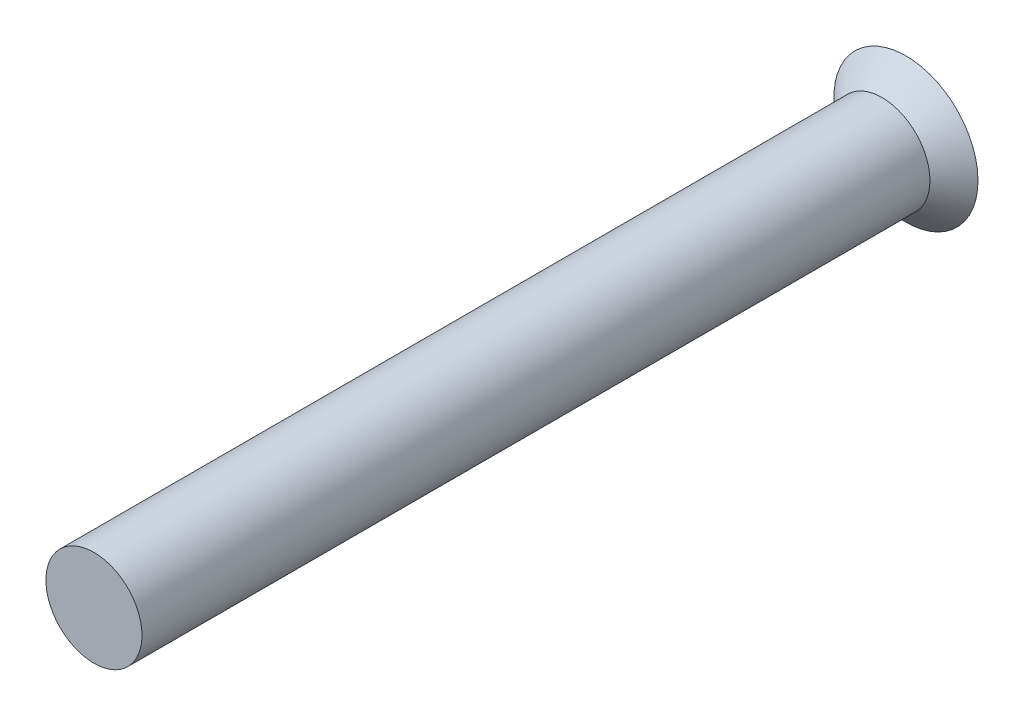
SolidWorks part; units mm, degrees
material "AISI 1020 Steel, Cold Rolled"
ref_plane "Front Plane" through (0, 0, 0) normal (0, 0, 1) x (1, 0, 0)
ref_plane "Top Plane" through (0, 0, 0) normal (0, 1, 0) x (1, 0, 0)
ref_plane "Right Plane" through (0, 0, 0) normal (1, 0, 0) x (0, 0, -1)
sketch "Sketch1" plane through (0, 0, 0) normal (0, 0, 1) x (1, 0, 0)
  circle A0 centre (0, 0) radius 0.5
  dimension "D1" = 1
extrude "Boss-Extrude1" add sketch "Sketch1" along normal mid plane 8.2 contours A0
sketch "Sketch2" plane through (0, 0, 0) normal (1, 0, 0) x (0, 0, -1)
  line L1 (4.35, 0.75) -> (4.35, 0)
  line L2 (4.35, 0) -> (4.1, 0)
  line L3 (4.1, -0.5) -> (4.1, 0.5) construction
  line L4 (4.1, 0) -> (4.1, 0.5)
  line L5 (4.1, 0.5) -> (4.35, 0.75)
  dimension "D1" = 0.25
ref_axis "Axis1" through (0, 0, 2.0805) along (0, 0, -1)
revolve "Revolve1" add sketch "Sketch2" angle 360 about axis through (0, 0, 2.0805) along (0, 0, -1)
sketch "Sketch3" plane through (0, 0, -4.35) normal (0, 0, -1) x (-1, 0, 0)
  line L0 (0.1, 0.6) -> (-0.1, 0.6)
  line L1 (-0.1, 0.6) -> (-0.1, 0.1)
  line L2 (-0.1, 0.1) -> (-0.6, 0.1)
  line L3 (-0.6, 0.1) -> (-0.6, -0.1)
  line L4 (-0.6, -0.1) -> (-0.1056, -0.1)
  line L5 (-0.1056, -0.1) -> (-0.1056, -0.6)
  line L6 (-0.1056, -0.6) -> (0.1056, -0.6)
  line L7 (0.1056, -0.6) -> (0.1056, -0.1)
  line L8 (0.1056, -0.1) -> (0.6, -0.1)
  line L9 (0.6, -0.1) -> (0.6, 0.1)
  line L10 (0.6, 0.1) -> (0.1, 0.1)
  line L11 (0.1, 0.1) -> (0.1, 0.6)
  line L12 (0.825, 0) -> (-0.825, 0) construction
  line L13 (0, 0.825) -> (0, -0.825) construction
  point P11 (-0.6, 0)
  point P15 (0, -0.6)
  dimension "D1" = 0.5
  dimension "D2" = 0.5
  dimension "D3" = 0.2
  dimension "D4" = 0.2
extrude "Cut-Extrude1" cut sketch "Sketch3" against normal blind 0.1
